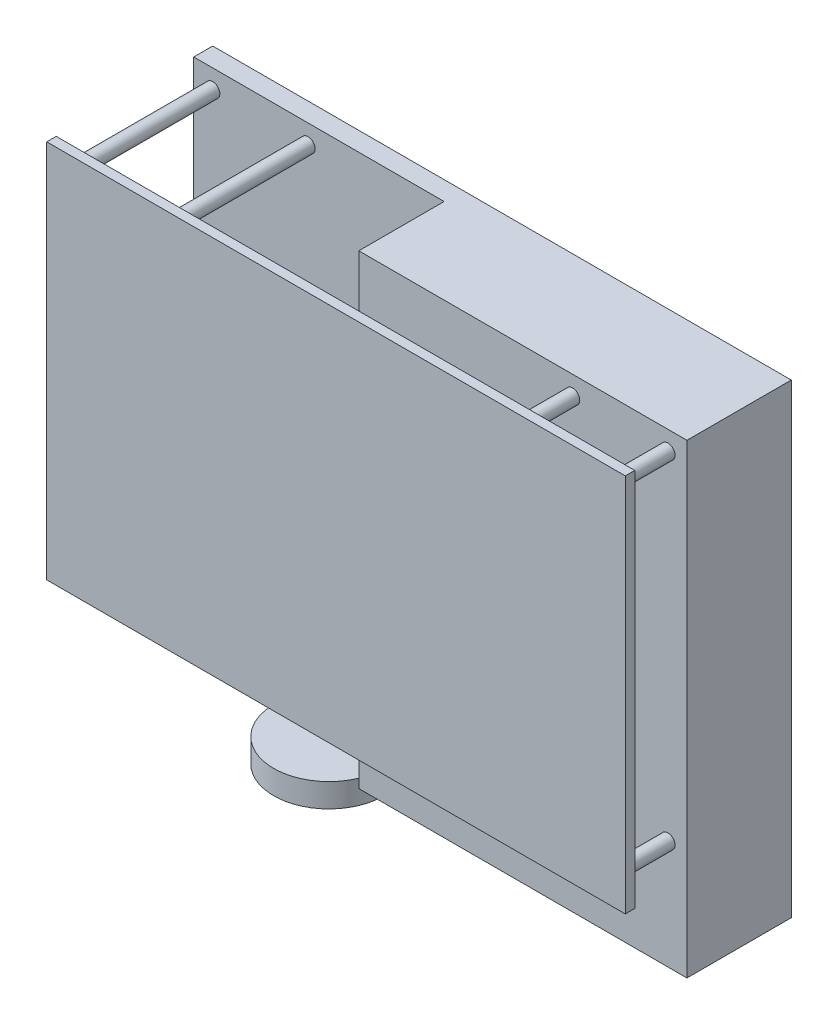
SolidWorks part; units mm, degrees
ref_plane "前视基准面" through (0, 0, 0) normal (0, 0, 1) x (1, 0, 0)
ref_plane "上视基准面" through (0, 0, 0) normal (0, 1, 0) x (1, 0, 0)
ref_plane "右视基准面" through (0, 0, 0) normal (1, 0, 0) x (0, 0, -1)
sketch "草图1" plane through (0, 0, 0) normal (0, 0, 1) x (1, 0, 0)
  line L1 (-61, 40) -> (61, 40)
  line L2 (-61, 40) -> (-61, -40)
  line L3 (-61, -40) -> (61, -40)
  line L4 (61, 40) -> (61, -40)
  line L5 (-61, 40) -> (61, -40) construction
  line L6 (-61, -40) -> (61, 40) construction
  point P0 (0, 0)
  dimension "D1" = 122
  dimension "D2" = 80
extrude "凸台-拉伸1" add sketch "草图1" along normal blind 2
sketch "草图2" plane through (0, 0, 2) normal (0, 0, 1) x (1, 0, 0)
  line L0 (61, 40) -> (-61, 40) construction
  line L2 (61, -40) -> (61, 40) construction
  circle A0 centre (-36.9, 36) radius 1.5
  circle A1 centre (-11.5, 36) radius 1.5
  circle A2 centre (57, 36) radius 1.5
  circle A3 centre (-11.5, -35.2) radius 1.5
  circle A4 centre (57, -35.2) radius 1.5
  dimension "D3" = 3
  dimension "D6" = 25.4
  dimension "D7" = 68.5
  dimension "D8" = 71.2
  dimension "D9" = 68.5
  dimension "D11" = 4
  dimension "D1" = 3
  dimension "D2" = 3
  dimension "D4" = 3
  dimension "D5" = 3
  dimension "D10" = 4
  dimension "D12" = 4
  dimension "D13" = 4
  dimension "D14" = 4
  dimension "D15" = 71.2
extrude "凸台-拉伸3" add sketch "草图2" against normal blind 31 contours A4 | A3 | A2 | A0
sketch "草图5" plane through (0, 0, -29) normal (0, 0, -1) x (-1, 0, 0)
  line L1 (-61, 40) -> (61, 40)
  line L2 (-61, 40) -> (-61, -58.2)
  line L3 (-61, -58.2) -> (61, -58.2)
  line L4 (61, 40) -> (61, -58.2)
  dimension "D1" = 122
  dimension "D2" = 98.2
extrude "凸台-拉伸5" add sketch "草图5" along normal blind 4
ref_plane "基准面1" through (0, 0, 0) normal (0, 1, 0) x (1, 0, 0)
ref_plane "基准面2" through (0, 0, 0) normal (1, 0, 0) x (0, 0, -1)
mirror "镜向2" about plane through (0, 0, 0) normal (1, 0, 0) of "凸台-拉伸3"
sketch "草图6" plane through (0, 0, -29) normal (0, 0, 1) x (1, 0, 0)
  line L0 (61, -58.2) -> (-61, -58.2) construction
  line L1 (61, 40) -> (-8.2, 40)
  line L2 (61, 40) -> (61, -58.2)
  line L3 (61, -58.2) -> (-8.2, -58.2)
  line L4 (-8.2, 40) -> (-8.2, -58.2)
  dimension "D1" = 69.2
extrude "凸台-拉伸6" add sketch "草图6" along normal blind 18
sketch "草图7" plane through (0, -58.2, 0) normal (0, -1, 0) x (1, 0, 0)
  line L0 (-8.2, -29) -> (-61, -29) construction
  line L1 (-8.2, -11) -> (-8.2, -29) construction
  circle A0 centre (-20.85, -17.35) radius 11.65
  dimension "D1" = 23.3
  dimension "D2" = 12.65
extrude "凸台-拉伸9" add sketch "草图7" along normal blind 5 separate body
